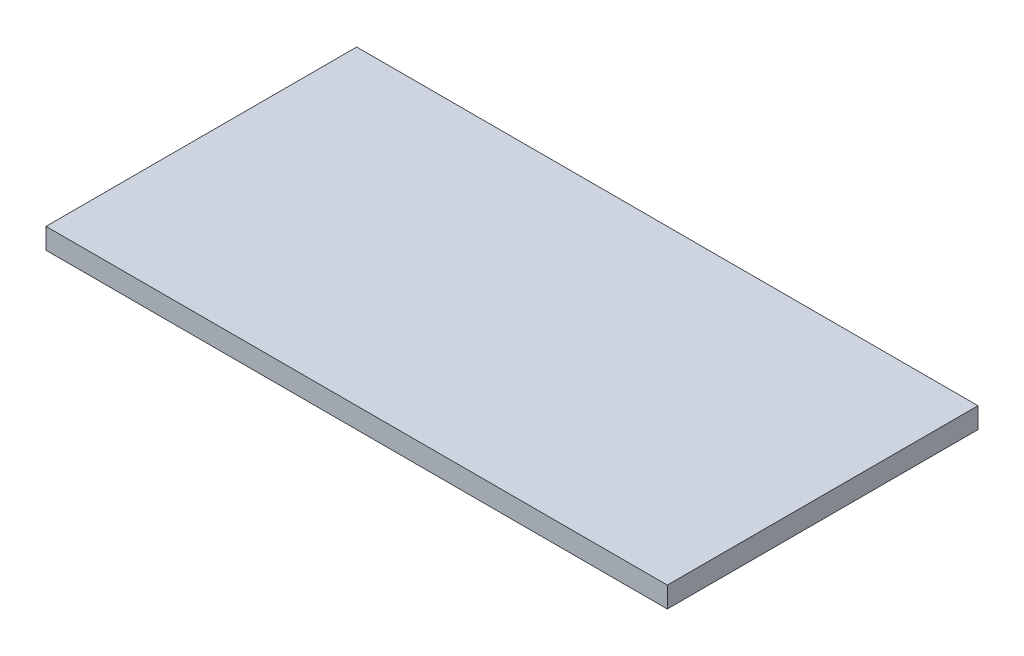
SolidWorks part; units mm, degrees
ref_plane "Front Plane" through (0, 0, 0) normal (0, 0, 1) x (1, 0, 0)
ref_plane "Top Plane" through (0, 0, 0) normal (0, 1, 0) x (1, 0, 0)
ref_plane "Right Plane" through (0, 0, 0) normal (1, 0, 0) x (0, 0, -1)
sketch "Sketch1" plane through (0, 0, 0) normal (0, 1, 0) x (1, 0, 0)
  line L1 (-13.3, 6.6) -> (16.7, 6.6)
  line L2 (-13.3, 6.6) -> (-13.3, -8.4)
  line L3 (-13.3, -8.4) -> (16.7, -8.4)
  line L4 (16.7, 6.6) -> (16.7, -8.4)
  line L5 (-13.3, 6.6) -> (16.7, -8.4) construction
  line L6 (-13.3, -8.4) -> (16.7, 6.6) construction
  point P4 (1.7, -0.9)
  dimension "D1" = 15
  dimension "D2" = 30
extrude "Boss-Extrude1" add sketch "Sketch1" along normal blind 1
